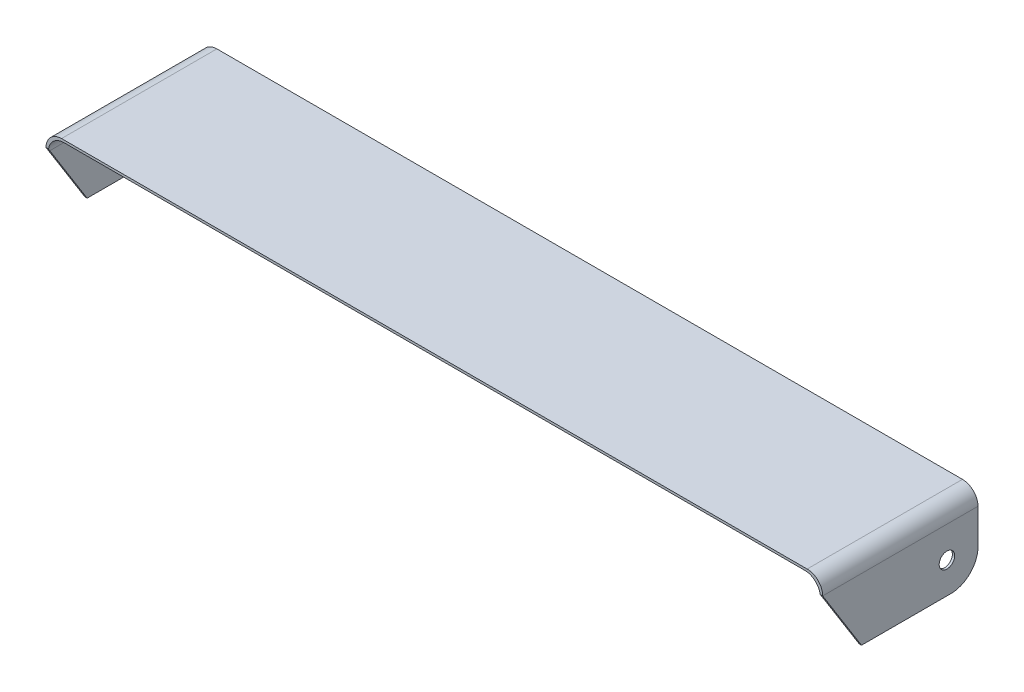
SolidWorks part; units mm, degrees
ref_plane "Front Plane" through (0, 0, 0) normal (0, 0, 1) x (1, 0, 0)
ref_plane "Top Plane" through (0, 0, 0) normal (0, 1, 0) x (1, 0, 0)
ref_plane "Right Plane" through (0, 0, 0) normal (1, 0, 0) x (0, 0, -1)
sketch "Sketch2" plane through (0, 0, 0) normal (0, 0, 1) x (1, 0, 0)
  line L0 (0, 0) -> (0, 80)
  line L1 (20, 100) -> (980, 100)
  line L2 (1000, 80) -> (1000, 0)
  line L3 (3, 0) -> (3, 77)
  line L4 (23, 97) -> (977, 97)
  line L5 (997, 77) -> (997, 0)
  line L6 (0, 0) -> (3, 0)
  line L7 (997, 0) -> (1000, 0)
  line L8 (1000, 100) -> (1000, 0) construction
  line L9 (0, 100) -> (1000, 100) construction
  line L10 (997, 97) -> (997, 0) construction
  line L11 (3, 97) -> (997, 97) construction
  line L12 (0, 0) -> (0, 100) construction
  line L13 (3, 0) -> (3, 97) construction
  arc A0 (1000, 80) -> (980, 100) centre (980, 80) ccw
  arc A1 (997, 77) -> (977, 97) centre (977, 77) ccw
  arc A2 (20, 100) -> (0, 80) centre (20, 80) ccw
  arc A3 (23, 97) -> (3, 77) centre (23, 77) ccw
  point P12 (1000, 100)
  dimension "D4" = 20
  dimension "D5" = 20
  dimension "D1" = 3
extrude "Boss-Extrude1" add sketch "Sketch2" along normal mid plane 200
sketch "Sketch3" plane through (1000, 0, 0) normal (1, 0, 0) x (0, 0, -1)
  line L0 (-100, 0) -> (-50, 0)
  line L1 (-100, 0) -> (100, 0) construction
  line L2 (-50, 0) -> (-100, 80)
  line L3 (-100, 0) -> (-100, 80) construction
  line L4 (-100, 80) -> (-100, 0)
  dimension "D1" = 50
  dimension "D2" = 80
extrude "Cut-Extrude1" cut sketch "Sketch3" against normal through all
sketch "Sketch4" plane through (1000, 0, 0) normal (1, 0, 0) x (0, 0, -1)
  line L0 (100, 0) -> (100, 80) construction
  line L2 (-100, 100) -> (100, 100) construction
  circle A0 centre (60, 40) radius 10
  dimension "D3" = 20
  dimension "D1" = 40
  dimension "D2" = 60
extrude "Cut-Extrude2" cut sketch "Sketch4" against normal through all
fillet "Fillet3" radius 35 2 edges at (998.5, 0, -100) (1.5, 0, -100)
